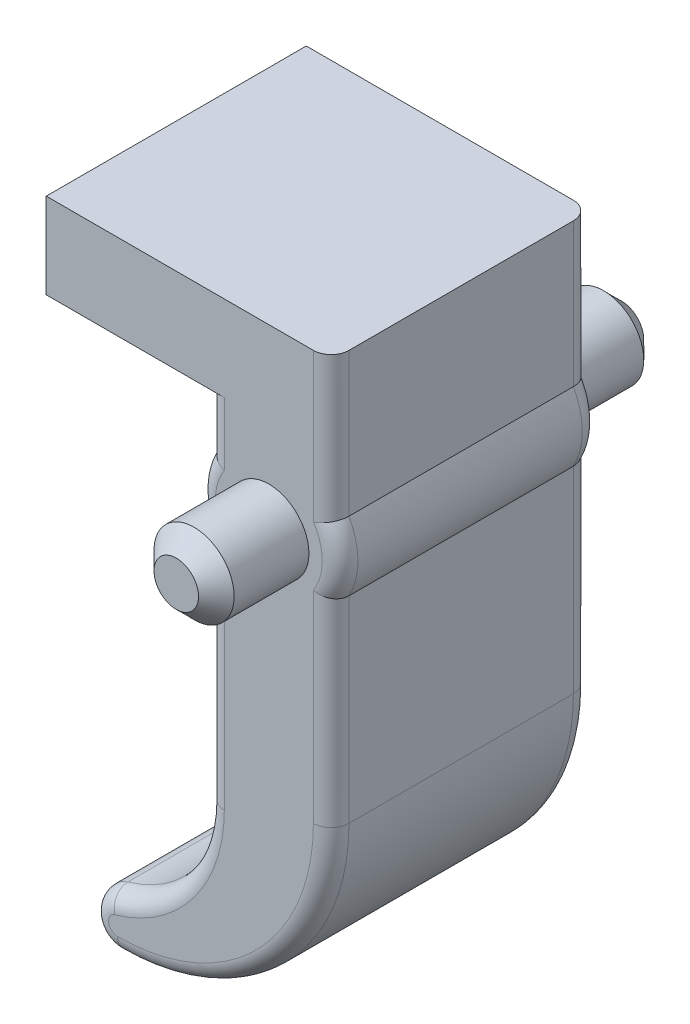
SolidWorks part; units mm, degrees
ref_plane "Plan de face" through (0, 0, 0) normal (0, 0, 1) x (1, 0, 0)
ref_plane "Plan de dessus" through (0, 0, 0) normal (0, 1, 0) x (1, 0, 0)
ref_plane "Plan de droite" through (0, 0, 0) normal (1, 0, 0) x (0, 0, -1)
sketch "Esquisse1" plane through (0, 0, 0) normal (0, 0, 1) x (1, 0, 0)
  line L0 (-3.5, 1.9365) -> (3.5, 1.9365) construction
  line L2 (-3.5, -1.9365) -> (-3.5, -14.8542)
  line L4 (3.5, -1.9365) -> (3.5, -13)
  line L5 (-3.5, -1.9365) -> (3.5, -1.9365) construction
  line L7 (-3.5, 1.9365) -> (-3.5, 5.2)
  line L8 (-3.5, 10) -> (3.5, 10)
  line L9 (3.5, 1.9365) -> (3.5, 10)
  line L10 (-3.5, 10) -> (-12.5, 10)
  line L12 (-3.5, 5.2) -> (-12.5, 5.2)
  line L13 (-12.5, 10) -> (-12.5, 5.2)
  arc A0 (3.5, -1.9365) -> (3.5, 1.9365) centre (0, 0) ccw
  arc A1 (-8.9167, -22.059) -> (-3.5, -14.8542) centre (-11, -14.8542) ccw
  arc A2 (-8.9167, -22.059) -> (-8.5, -25) centre (-8.5, -23.5) ccw
  arc A3 (-8.5, -25) -> (3.5, -13) centre (-8.5, -13) ccw
  arc A4 (-3.5, 1.9365) -> (-3.5, -1.9365) centre (0, 0) ccw
  dimension "D1" = 8
  dimension "D2" = 7
  dimension "6" = 3
  dimension "D4" = 7.5
  dimension "D5" = 12
  dimension "D3" = 25
  dimension "D6" = 8.5
  dimension "D7" = 10
  dimension "D8" = 16
  dimension "D9" = 4.8
extrude "Boss.-Extru.1" add sketch "Esquisse1" along normal mid plane 14.6
sketch "Esquisse2" plane through (0, 0, 7.3) normal (0, 0, 1) x (1, 0, 0)
  circle A0 centre (0, 0) radius 2.25
  dimension "D1" = 4.5
extrude "Boss.-Extru.2" add sketch "Esquisse2" along normal blind 5.2
chamfer "Chanfrein1" distance 1 angle 45 1 edges at (2.25, 0, 12.5)
mirror "Symétrie1" about plane through (0, 0, 0) normal (0, 0, 1) of "Boss.-Extru.2"
chamfer "Chanfrein2" distance 1 angle 45 1 edges at (2.25, 0, -12.5)
fillet "Congé1" radius 1 18 edges at (3.5, -7.4682, 7.3) (-0.0147, -21.4853, 7.3) (-9.9852, -23.7104, 7.3) (-5.0052, -19.3611, 7.3) (-3.5, -8.3953, -7.3) (-5.0052, -19.3611, -7.3) (-9.9852, -23.7104, -7.3) (-0.0147, -21.4853, -7.3) (3.5, 5.9682, 7.3) (4, 0, 7.3) (-3.5, -8.3953, 7.3) (-4, 0, 7.3) (-3.5, 3.5682, 7.3) (-3.5, 3.5682, -7.3) (-4, 0, -7.3) (3.5, -7.4682, -7.3) (4, 0, -7.3) (3.5, 5.9682, -7.3)
